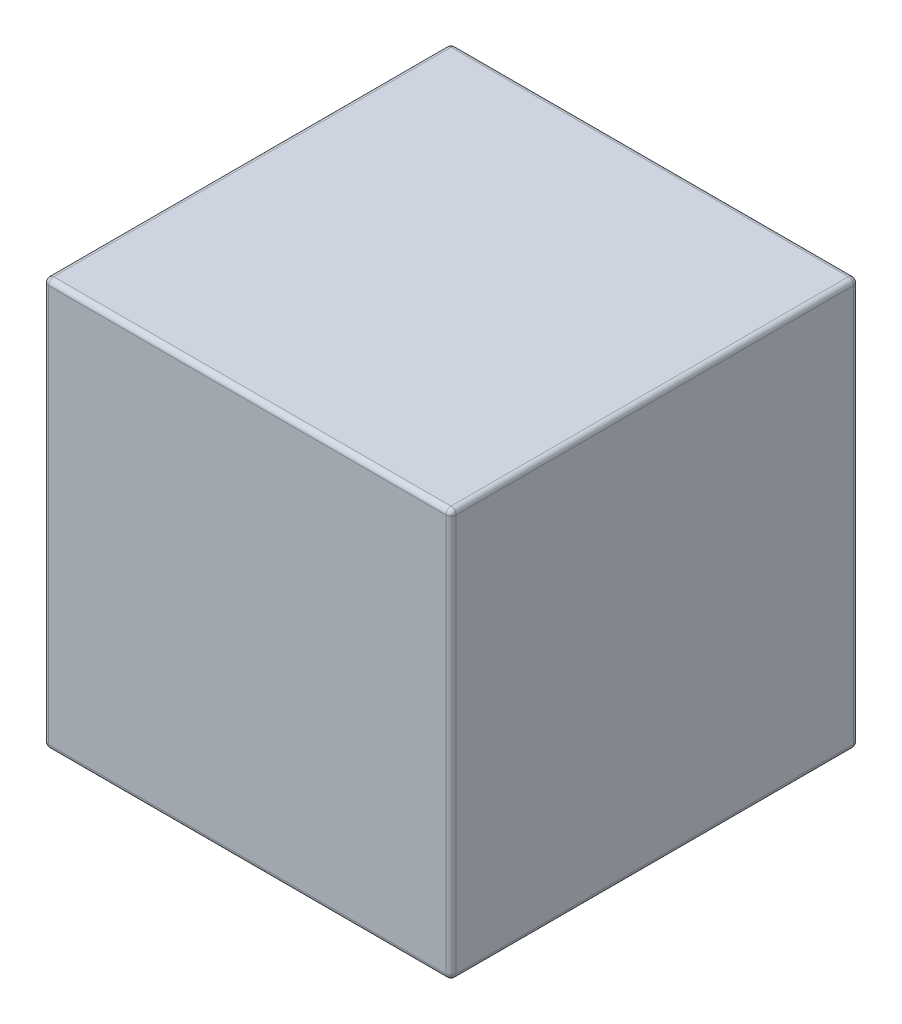
SolidWorks part; units mm, degrees
ref_plane "Front Plane" through (0, 0, 0) normal (0, 0, 1) x (1, 0, 0)
ref_plane "Top Plane" through (0, 0, 0) normal (0, 1, 0) x (1, 0, 0)
ref_plane "Right Plane" through (0, 0, 0) normal (1, 0, 0) x (0, 0, -1)
sketch "Sketch1" plane through (0, 0, 0) normal (0, 1, 0) x (1, 0, 0)
  line L1 (-25.4, -25.4) -> (25.4, -25.4)
  line L2 (-25.4, -25.4) -> (-25.4, 25.4)
  line L3 (-25.4, 25.4) -> (25.4, 25.4)
  line L4 (25.4, -25.4) -> (25.4, 25.4)
  line L5 (-25.4, -25.4) -> (25.4, 25.4) construction
  line L6 (-25.4, 25.4) -> (25.4, -25.4) construction
  point P0 (0, 0)
  dimension "D1" = 50.8
  dimension "D2" = 50.8
extrude "Boss-Extrude1" add sketch "Sketch1" along normal blind 50.8
fillet "Fillet1" radius 0.635 12 edges at (-25.4, 25.4, -25.4) (0, 0, -25.4) (-25.4, 0, 0) (25.4, 25.4, -25.4) (25.4, 0, 0) (-25.4, 50.8, 0) (0, 50.8, -25.4) (25.4, 50.8, 0) (-25.4, 25.4, 25.4) (0, 50.8, 25.4) (25.4, 25.4, 25.4) (0, 0, 25.4)
